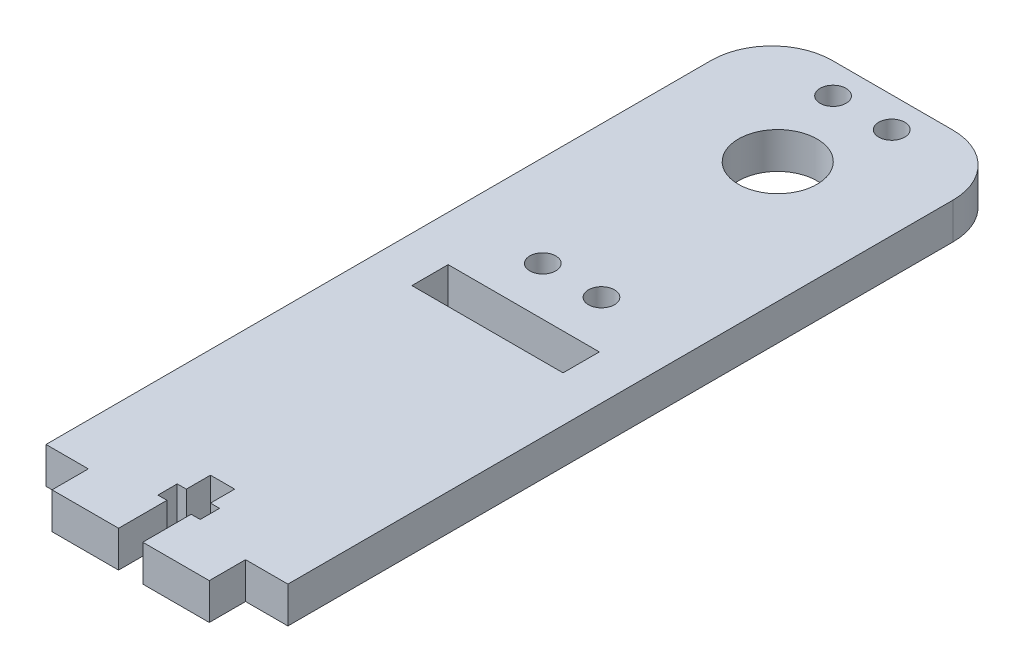
SolidWorks part; units mm, degrees
ref_plane "Front Plane" through (0, 0, 0) normal (0, 0, 1) x (1, 0, 0)
ref_plane "Top Plane" through (0, 0, 0) normal (0, 1, 0) x (1, 0, 0)
ref_plane "Right Plane" through (0, 0, 0) normal (1, 0, 0) x (0, 0, -1)
sketch "Sketch1" plane through (0, 0, 0) normal (0, 1, 0) x (1, 0, 0)
  line L0 (-20, -60) -> (-13, -60) construction
  line L1 (-10, 60) -> (10, 60)
  line L2 (-20, 50) -> (-20, -60)
  line L3 (-20, -60) -> (-13, -60)
  line L4 (20, 50) -> (20, -60)
  line L5 (-20, 60) -> (20, -60) construction
  line L6 (-20, -60) -> (20, 60) construction
  line L7 (-13, -60) -> (-13, -66)
  line L8 (-13, -66) -> (-2, -66)
  line L9 (13, -66) -> (13, -60)
  line L10 (0, 60) -> (0, 55) construction
  line L11 (-4.85, 55) -> (4.85, 55) construction
  line L12 (0, 60) -> (0, 41) construction
  line L13 (4.85, 55) -> (4.85, 7) construction
  line L14 (-4.85, 55) -> (-4.85, 7) construction
  line L15 (13, -60) -> (20, -60)
  line L16 (-20, -60) -> (-20, -40) construction
  line L17 (-20, -60) -> (-20, 0) construction
  line L18 (-2, -66) -> (-2, -58)
  line L19 (-2, -58) -> (-3.5, -58)
  line L20 (-3.5, -58) -> (-3.5, -54.8)
  line L21 (-3.5, -54.8) -> (-2, -54.8)
  line L22 (3.5, -54.8) -> (3.5, -58)
  line L23 (3.5, -58) -> (2, -58)
  line L24 (2, -58) -> (2, -66)
  line L25 (-2, -54.8) -> (-2, -50.8)
  line L26 (-2, -50.8) -> (2, -50.8)
  line L27 (2, -50.8) -> (2, -54.8)
  line L28 (2, -54.8) -> (3.5, -54.8)
  line L29 (2, -66) -> (13, -66)
  line L30 (0, 55) -> (0, 58) construction
  line L31 (-10, 58) -> (10, 58) construction
  line L32 (10, 58) -> (10, 4) construction
  line L33 (10, 4) -> (0, 4) construction
  line L34 (-10, 58) -> (-10, 4) construction
  line L35 (-10, 4) -> (0, 4) construction
  line L36 (0, 4) -> (0, -4) construction
  line L38 (-12.5, -1) -> (12.5, -1)
  line L39 (-12.5, -1) -> (-12.5, -7)
  line L40 (-12.5, -7) -> (12.5, -7)
  line L41 (12.5, -1) -> (12.5, -7)
  line L42 (-12.5, -1) -> (12.5, -7) construction
  line L43 (-12.5, -7) -> (12.5, -1) construction
  arc A0 (10, 60) -> (20, 50) centre (10, 50) cw
  arc A1 (-10, 60) -> (-20, 50) centre (-10, 50) ccw
  circle A2 centre (4.85, 55) radius 2.15
  circle A3 centre (0, 41) radius 6.5
  circle A4 centre (4.85, 7) radius 2.15
  circle A5 centre (-4.85, 55) radius 2.15
  circle A6 centre (-4.85, 7) radius 2.15
  point P0 (0, 0)
  dimension "D5" = 10
  dimension "D6" = 4.3
  dimension "D7" = 4.3
  dimension "D8" = 13
  dimension "D1" = 40
  dimension "D2" = 120
  dimension "D3" = 26
  dimension "D4" = 7
  dimension "D9" = 5
  dimension "D10" = 14
  dimension "D11" = 48
  dimension "D12" = 6
  dimension "D13" = 4
  dimension "D14" = 3.2
  dimension "D15" = 7
  dimension "D16" = 8
  dimension "D17" = 4
  dimension "D18" = 20
  dimension "D19" = 60
  dimension "D20" = 20
  dimension "D21" = 54
  dimension "D22" = 6
  dimension "D23" = 25
  dimension "D24" = 2
  dimension "D25" = 4.85
  dimension "D26" = 56
extrude "Boss-Extrude1" add sketch "Sketch1" against normal blind 6
